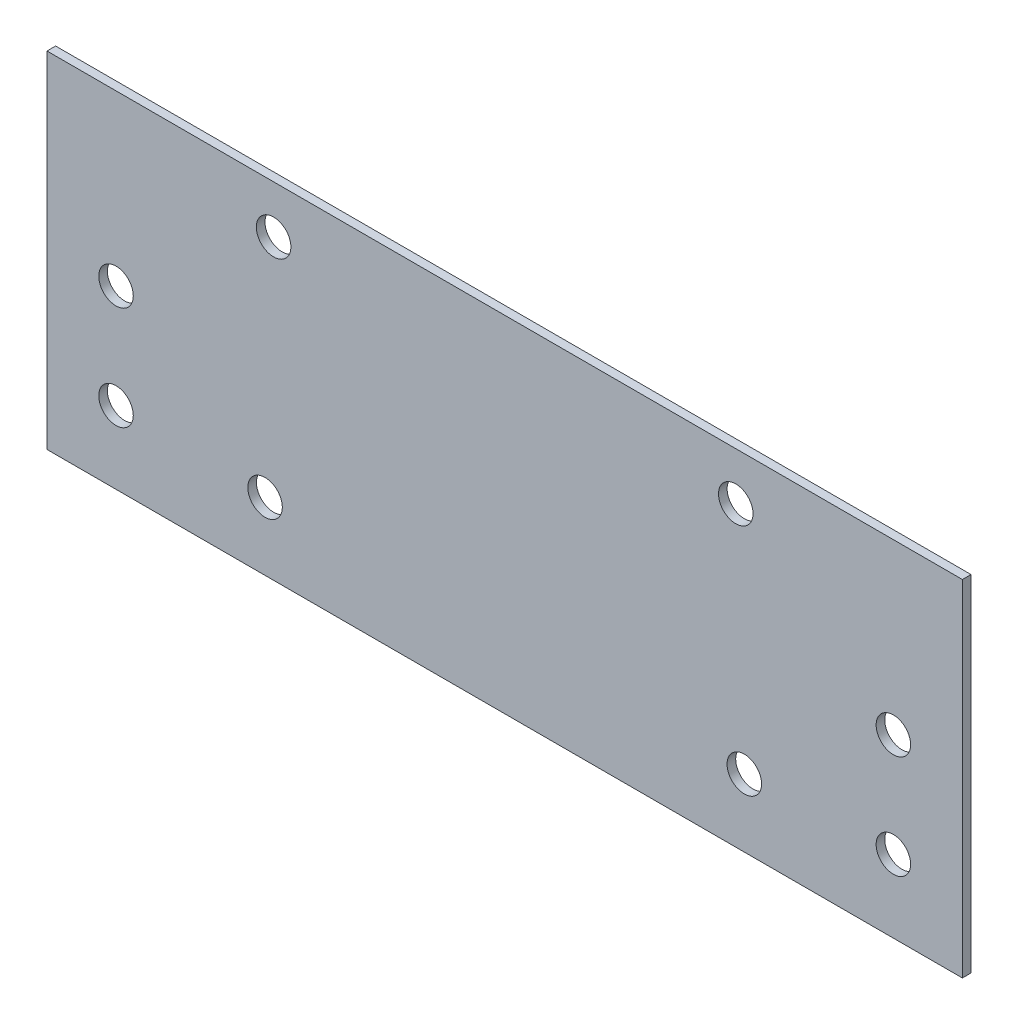
SolidWorks part; units mm, degrees
material "McMaster 6061-T6"
ref_plane "Front" through (0, 0, 0) normal (0, 0, 1) x (1, 0, 0)
ref_plane "Top" through (0, 0, 0) normal (0, 1, 0) x (1, 0, 0)
ref_plane "Right" through (0, 0, 0) normal (1, 0, 0) x (0, 0, -1)
sketch "Sketch1" plane through (0, 0, 0) normal (0, 0, 1) x (1, 0, 0)
  line L1 (84.2125, -31.75) -> (-84.2125, -31.75)
  line L2 (84.2125, -31.75) -> (84.2125, 31.75)
  line L3 (84.2125, 31.75) -> (-84.2125, 31.75)
  line L4 (-84.2125, -31.75) -> (-84.2125, 31.75)
  line L5 (84.2125, -31.75) -> (-84.2125, 31.75) construction
  line L6 (84.2125, 31.75) -> (-84.2125, -31.75) construction
  point P0 (0, 0)
  dimension "D1" = 168.425
  dimension "D2" = 63.5
extrude "Boss-Extrude1" add sketch "Sketch1" along normal blind 1.5875
sketch "Sketch2" plane through (0, 0, 1.5875) normal (0, 0, 1) x (1, 0, 0)
  line L0 (0, 0) -> (0, 31.75) construction
  circle A0 centre (-42.516, 22.9603) radius 3.175
  circle A1 centre (-44.0908, -19.3146) radius 3.175
  circle A4 centre (-71.5125, 0.6502) radius 3.175
  circle A5 centre (-71.5125, -18.3998) radius 3.175
  circle A6 centre (71.5149, 0.6502) radius 3.175
  circle A7 centre (71.5149, -18.3998) radius 3.175
  circle A8 centre (44.0908, -19.3146) radius 3.175
  circle A9 centre (42.516, 22.9603) radius 3.175
  dimension "D1" = 6.35
  dimension "D2" = 6.35
extrude "Cut-Extrude1" cut sketch "Sketch2" against normal through all
